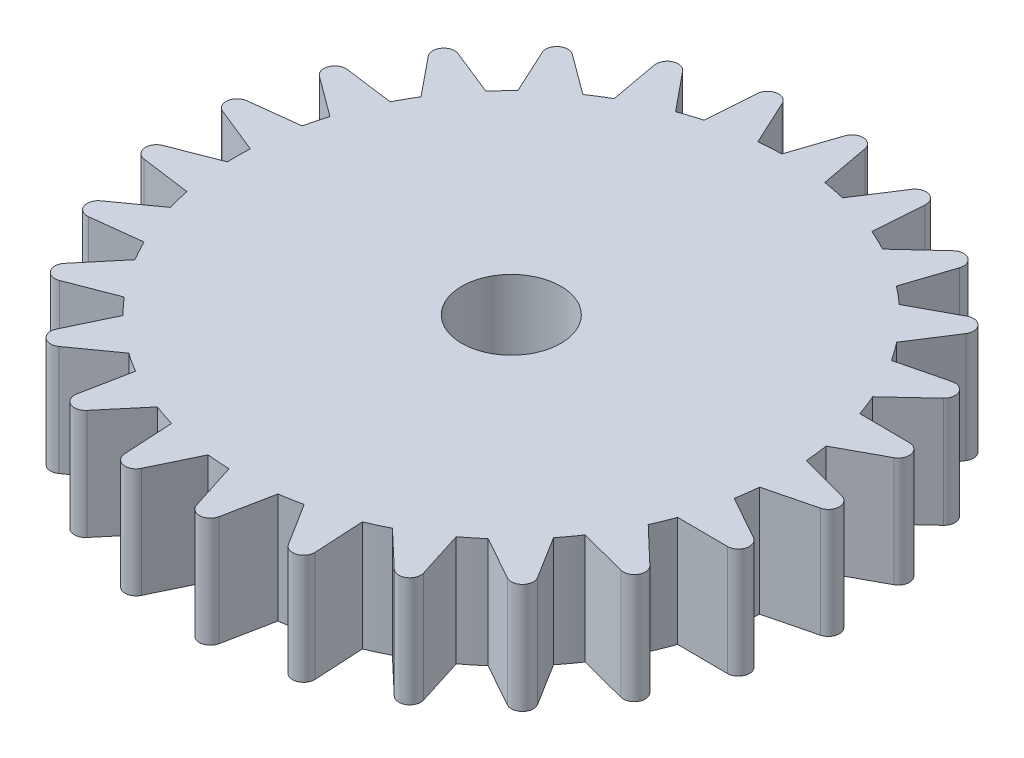
SolidWorks part; units mm, degrees
ref_plane "Front Plane" through (0, 0, 0) normal (0, 0, 1) x (1, 0, 0)
ref_plane "Top Plane" through (0, 0, 0) normal (0, 1, 0) x (1, 0, 0)
ref_plane "Right Plane" through (0, 0, 0) normal (1, 0, 0) x (0, 0, -1)
ref_plane "Plane1" through (0, -74.1, 0) normal (0, 1, 0) x (1, 0, 0)
sketch "Sketch1" plane through (0, -74.1, 0) normal (0, 1, 0) x (1, 0, 0)
  line L0 (-5.5734, -7.2496) -> (-3.9092, -5.7039)
  line L1 (-4.3699, -4.8523) -> (-6.5743, -5.3991)
  line L2 (-7.1726, -4.5637) -> (-5.9451, -2.6527)
  line L3 (-6.6031, -1.9424) -> (-8.6023, -3.0203)
  line L4 (-9.3894, -2.3599) -> (-8.6758, -0.2037)
  line L5 (-9.4897, 0.3207) -> (-11.1581, -1.2205)
  line L6 (-12.0847, -0.7767) -> (-11.9297, 1.4893)
  line L7 (-12.8485, 1.7947) -> (-14.0811, -0.1129)
  line L8 (-15.0891, 0.0865) -> (-15.5024, 2.3198)
  line L9 (-16.4683, 2.3872) -> (-17.1878, 0.2329)
  line L10 (-18.2137, 0.1754) -> (-19.1695, 2.2358)
  line L11 (-20.1218, 2.0609) -> (-20.2829, -0.2047)
  line L12 (-21.2623, -0.5155) -> (-22.7004, 1.2425)
  line L13 (-23.5793, 0.8362) -> (-23.172, -1.3982)
  line L14 (-24.0432, -1.9428) -> (-25.8734, -0.5978)
  line L15 (-26.6236, -1.2098) -> (-25.6734, -3.2728)
  line L16 (-26.3819, -4.0169) -> (-28.489, -3.1693)
  line L17 (-29.0635, -3.9487) -> (-27.6301, -5.7105)
  line L18 (-28.1312, -6.6075) -> (-30.383, -6.3105)
  line L19 (-30.7456, -7.2083) -> (-28.9191, -8.5583)
  line L20 (-29.1814, -9.5517) -> (-31.4363, -9.824)
  line L21 (-31.5642, -10.7838) -> (-29.4593, -11.6371)
  line L22 (-29.4663, -12.6646) -> (-31.5827, -13.4891)
  line L23 (-31.4679, -14.4505) -> (-29.2169, -14.7536)
  line L24 (-28.9682, -15.7505) -> (-30.813, -17.0754)
  line L25 (-30.4627, -17.9781) -> (-28.2071, -17.7119)
  line L26 (-27.7183, -18.6156) -> (-29.1756, -20.3577)
  line L27 (-28.6119, -21.1449) -> (-26.4933, -20.3261)
  line L28 (-25.7951, -21.0799) -> (-26.7734, -23.1297)
  line L29 (-26.0316, -23.7519) -> (-24.1832, -22.432)
  line L30 (-23.3195, -22.9885) -> (-23.7573, -25.2171)
  line L31 (-22.8841, -25.6354) -> (-21.422, -23.8972)
  line L32 (-20.4471, -24.2214) -> (-20.3169, -26.4889)
  line L33 (-19.367, -26.6769) -> (-18.3832, -24.6297)
  line L34 (-17.3582, -24.7013) -> (-16.6682, -26.8652)
  line L35 (-15.7015, -26.811) -> (-15.2576, -24.5835)
  line L36 (-14.2471, -24.3979) -> (-13.0406, -26.3222)
  line L37 (-12.1177, -26.0293) -> (-12.2418, -23.7614)
  line L38 (-11.3091, -23.3303) -> (-9.662, -24.8942)
  line L39 (-8.841, -24.3809) -> (-9.5251, -22.2152)
  line L40 (-8.729, -21.5657) -> (-6.7447, -22.6708)
  line L41 (-6.0771, -21.9695) -> (-7.2783, -20.0419)
  line L42 (-6.6688, -19.2148) -> (-4.472, -19.7917)
  line L43 (-3.9997, -18.9464) -> (-5.6426, -17.3781)
  line L44 (-5.2579, -16.4254) -> (-2.9866, -16.4379)
  line L45 (-2.7395, -15.5017) -> (-4.7208, -14.3913)
  line L46 (-4.585, -13.3728) -> (-2.382, -12.82)
  line L47 (-2.3754, -11.8518) -> (-4.5706, -11.269)
  line L48 (-4.6924, -10.2488) -> (-2.6962, -9.1655)
  line L49 (-2.9305, -8.2261) -> (-5.2017, -8.2075)
  arc A0 (-3.9092, -5.7039) -> (-4.3699, -4.8523) centre (-4.2495, -5.3376) ccw
  arc A1 (-6.5743, -5.3991) -> (-7.1726, -4.5637) centre (-17.0034, -12.236) ccw
  arc A2 (-5.9451, -2.6527) -> (-6.6031, -1.9424) centre (-6.3658, -2.3825) ccw
  arc A3 (-8.6023, -3.0203) -> (-9.3894, -2.3599) centre (-17.0034, -12.236) ccw
  arc A4 (-8.6758, -0.2037) -> (-9.4897, 0.3207) centre (-9.1504, -0.0466) ccw
  arc A5 (-11.1581, -1.2205) -> (-12.0847, -0.7767) centre (-17.0034, -12.236) ccw
  arc A6 (-11.9297, 1.4893) -> (-12.8485, 1.7947) centre (-12.4285, 1.5234) ccw
  arc A7 (-14.0811, -0.1129) -> (-15.0891, 0.0865) centre (-17.0034, -12.236) ccw
  arc A8 (-15.5024, 2.3198) -> (-16.4683, 2.3872) centre (-15.9941, 2.2288) ccw
  arc A9 (-17.1878, 0.2329) -> (-18.2137, 0.1754) centre (-17.0034, -12.236) ccw
  arc A10 (-19.1695, 2.2358) -> (-20.1218, 2.0609) centre (-19.623, 2.0254) ccw
  arc A11 (-20.2829, -0.2047) -> (-21.2623, -0.5155) centre (-17.0034, -12.236) ccw
  arc A12 (-22.7004, 1.2425) -> (-23.5793, 0.8362) centre (-23.0874, 0.9259) ccw
  arc A13 (-23.172, -1.3982) -> (-24.0432, -1.9428) centre (-17.0034, -12.236) ccw
  arc A14 (-25.8734, -0.5978) -> (-26.6236, -1.2098) centre (-26.1695, -1.0007) ccw
  arc A15 (-25.6734, -3.2728) -> (-26.3819, -4.0169) centre (-17.0034, -12.236) ccw
  arc A16 (-28.489, -3.1693) -> (-29.0635, -3.9487) centre (-28.6756, -3.6332) ccw
  arc A17 (-27.6301, -5.7105) -> (-28.1312, -6.6075) centre (-17.0034, -12.236) ccw
  arc A18 (-30.383, -6.3105) -> (-30.7456, -7.2083) centre (-30.4484, -6.8062) ccw
  arc A19 (-28.9191, -8.5583) -> (-29.1814, -9.5517) centre (-17.0034, -12.236) ccw
  arc A20 (-31.4363, -9.824) -> (-31.5642, -10.7838) centre (-31.3763, -10.3204) ccw
  arc A21 (-29.4593, -11.6371) -> (-29.4663, -12.6646) centre (-17.0034, -12.236) ccw
  arc A22 (-31.5827, -13.4891) -> (-31.4679, -14.4505) centre (-31.4011, -13.955) ccw
  arc A23 (-29.2169, -14.7536) -> (-28.9682, -15.7505) centre (-17.0034, -12.236) ccw
  arc A24 (-30.813, -17.0754) -> (-30.4627, -17.9781) centre (-30.5213, -17.4816) ccw
  arc A25 (-28.2071, -17.7119) -> (-27.7183, -18.6156) centre (-17.0034, -12.236) ccw
  arc A26 (-29.1756, -20.3577) -> (-28.6119, -21.1449) centre (-28.7921, -20.6785) ccw
  arc A27 (-26.4933, -20.3261) -> (-25.7951, -21.0799) centre (-17.0034, -12.236) ccw
  arc A28 (-26.7734, -23.1297) -> (-26.0316, -23.7519) centre (-26.3222, -23.345) ccw
  arc A29 (-24.1832, -22.432) -> (-23.3195, -22.9885) centre (-17.0034, -12.236) ccw
  arc A30 (-23.7573, -25.2171) -> (-22.8841, -25.6354) centre (-23.2667, -25.3135) ccw
  arc A31 (-21.422, -23.8972) -> (-20.4471, -24.2214) centre (-17.0034, -12.236) ccw
  arc A32 (-20.3169, -26.4889) -> (-19.367, -26.6769) centre (-19.8177, -26.4603) ccw
  arc A33 (-18.3832, -24.6297) -> (-17.3582, -24.7013) centre (-17.0034, -12.236) ccw
  arc A34 (-16.6682, -26.8652) -> (-15.7015, -26.811) centre (-16.1918, -26.7133) ccw
  arc A35 (-15.2576, -24.5835) -> (-14.2471, -24.3979) centre (-17.0034, -12.236) ccw
  arc A36 (-13.0406, -26.3222) -> (-12.1177, -26.0293) centre (-12.617, -26.0566) ccw
  arc A37 (-12.2418, -23.7614) -> (-11.3091, -23.3303) centre (-17.0034, -12.236) ccw
  arc A38 (-9.662, -24.8942) -> (-8.841, -24.3809) centre (-9.3177, -24.5316) ccw
  arc A39 (-9.5251, -22.2152) -> (-8.729, -21.5657) centre (-17.0034, -12.236) ccw
  arc A40 (-6.7447, -22.6708) -> (-6.0771, -21.9695) centre (-6.5014, -22.2339) ccw
  arc A41 (-7.2783, -20.0419) -> (-6.6688, -19.2148) centre (-17.0034, -12.236) ccw
  arc A42 (-4.472, -19.7917) -> (-3.9997, -18.9464) centre (-4.345, -19.3081) ccw
  arc A43 (-5.6426, -17.3781) -> (-5.2579, -16.4254) centre (-17.0034, -12.236) ccw
  arc A44 (-2.9866, -16.4379) -> (-2.7395, -15.5017) centre (-2.9839, -15.9379) ccw
  arc A45 (-4.7208, -14.3913) -> (-4.585, -13.3728) centre (-17.0034, -12.236) ccw
  arc A46 (-2.382, -12.82) -> (-2.3754, -11.8518) centre (-2.5037, -12.3351) ccw
  arc A47 (-4.5706, -11.269) -> (-4.6924, -10.2488) centre (-17.0034, -12.236) ccw
  arc A48 (-2.6962, -9.1655) -> (-2.9305, -8.2261) centre (-2.9346, -8.726) ccw
  arc A49 (-5.2017, -8.2075) -> (-5.5734, -7.2496) centre (-17.0034, -12.236) ccw
extrude "Boss-Extrude1" add sketch "Sketch1" against normal blind 5
sketch "Sketch6" plane through (0, -74.1, 0) normal (0, 1, 0) x (1, 0, 0)
  circle A0 centre (-17.0034, -12.236) radius 2.25
  dimension "D1" = 4.5
extrude "Cut-Extrude1" cut sketch "Sketch6" against normal through all
